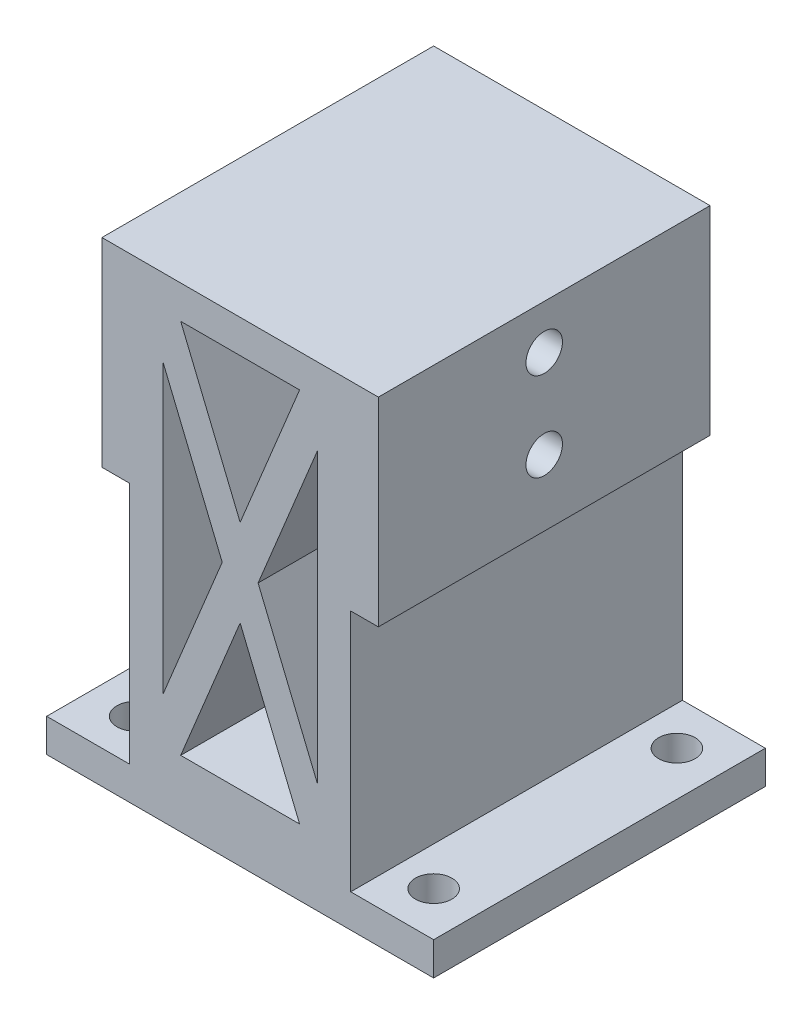
SolidWorks part; units mm, degrees
ref_plane "Front Plane" through (0, 0, 0) normal (0, 0, 1) x (1, 0, 0)
ref_plane "Top Plane" through (0, 0, 0) normal (0, 1, 0) x (1, 0, 0)
ref_plane "Right Plane" through (0, 0, 0) normal (1, 0, 0) x (0, 0, -1)
sketch "Sketch1" plane through (0, 0, 0) normal (0, 1, 0) x (1, 0, 0)
  line L1 (-17.5, -15) -> (17.5, -15)
  line L2 (-17.5, -15) -> (-17.5, 15)
  line L3 (-17.5, 15) -> (17.5, 15)
  line L4 (17.5, -15) -> (17.5, 15)
  line L5 (-17.5, -15) -> (17.5, 15) construction
  line L6 (-17.5, 15) -> (17.5, -15) construction
  point P0 (0, 0)
  dimension "D1" = 35
  dimension "D2" = 30
extrude "Boss-Extrude1" add sketch "Sketch1" along normal mid plane 3
sketch "Sketch2" plane through (0, 1.5, 0) normal (0, 1, 0) x (1, 0, 0)
  line L0 (17.5, 15) -> (-17.5, 15) construction
  line L1 (-17.5, 15) -> (-17.5, -15) construction
  line L2 (0, 0) -> (-5.8518, 0) construction
  line L3 (0, 0) -> (0, -5.0733) construction
  circle A0 centre (-13.5, 11) radius 1.65
  circle A1 centre (13.5, 11) radius 1.65
  circle A2 centre (13.5, -11) radius 1.65
  circle A3 centre (-13.5, -11) radius 1.65
  dimension "D1" = 3.3
  dimension "D2" = 4
  dimension "D3" = 4
extrude "Cut-Extrude1" cut sketch "Sketch2" against normal up to surface (3 mm away) up to face at (0, -1.5, 0)
sketch "Sketch3" plane through (0, 1.5, 0) normal (0, 1, 0) x (1, 0, 0)
  line L0 (17.5, 15) -> (-17.5, 15) construction
  line L1 (-10, -15) -> (10, -15)
  line L2 (-10, -15) -> (-10, 15)
  line L3 (-10, 15) -> (10, 15)
  line L4 (10, -15) -> (10, 15)
  line L5 (-10, -15) -> (10, 15) construction
  line L6 (-10, 15) -> (10, -15) construction
  point P0 (0, 0)
  dimension "D1" = 20
extrude "Boss-Extrude2" add sketch "Sketch3" along normal blind 40
sketch "Sketch4" plane through (10, 0, 0) normal (1, 0, 0) x (0, 0, -1)
  line L0 (0, 0) -> (0, -10.1706) construction
  line L2 (-15, 41.5) -> (-15, 1.5) construction
  line L3 (15, 41.5) -> (-15, 41.5)
  line L4 (15, 41.5) -> (15, 23.5)
  line L5 (15, 23.5) -> (-15, 23.5)
  line L6 (-15, 41.5) -> (-15, 23.5)
  dimension "D1" = 18
extrude "Boss-Extrude3" add sketch "Sketch4" along normal blind 2.5
mirror "Mirror1" about plane through (0, 0, 0) normal (1, 0, 0) of "Boss-Extrude3"
sketch "Sketch5" plane through (0, 0, -15) normal (0, 0, -1) x (-1, 0, 0)
  line L0 (-10, 23.5) -> (-10, 1.5) construction
  line L1 (7, 38.5) -> (-7, 38.5)
  line L2 (7, 38.5) -> (7, 4.5)
  line L3 (7, 4.5) -> (-7, 4.5)
  line L4 (-7, 38.5) -> (-7, 4.5)
  line L5 (7, 38.5) -> (-7, 4.5) construction
  line L6 (7, 4.5) -> (-7, 38.5) construction
  line L7 (10, 23.5) -> (10, 1.5) construction
  line L8 (-12.5, 41.5) -> (12.5, 41.5) construction
  line L9 (-17.5, 1.5) -> (-10, 1.5) construction
  line L10 (5.3778, 4.5) -> (-7, 34.5604)
  line L11 (7, 8.4396) -> (-5.3778, 38.5)
  line L12 (-7, 8.4396) -> (5.3778, 38.5)
  line L13 (7, 34.5604) -> (-5.3778, 4.5)
  point P0 (0, 21.5)
  dimension "D1" = 3
  dimension "D2" = 3
  dimension "D3" = 3
  dimension "D4" = 3
  dimension "D5" = 1.5
  dimension "D6" = 3
  dimension "D7" = 1.5
  dimension "D8" = 3
extrude "Cut-Extrude2" cut sketch "Sketch5" against normal up to surface (30 mm away) contours L11 L12 L1 | L2 L13 L11 | L4 L12 L10 | L10 L13 L3 up to face at (0, 15, 15)
sketch "Sketch7" plane through (-12.5, 0, 0) normal (-1, 0, 0) x (0, 0, 1)
  line L0 (-15, 41.5) -> (15, 41.5) construction
  line L1 (0, 0) -> (0, -4.3038) construction
  circle A0 centre (0, 37.5) radius 1.65
  circle A1 centre (0, 29.5) radius 1.65
  dimension "D1" = 3.3
  dimension "D2" = 4
  dimension "D3" = 8
extrude "Cut-Extrude3" cut sketch "Sketch7" against normal up to surface (25 mm away) up to face at (12.5, 32.5, 0)
